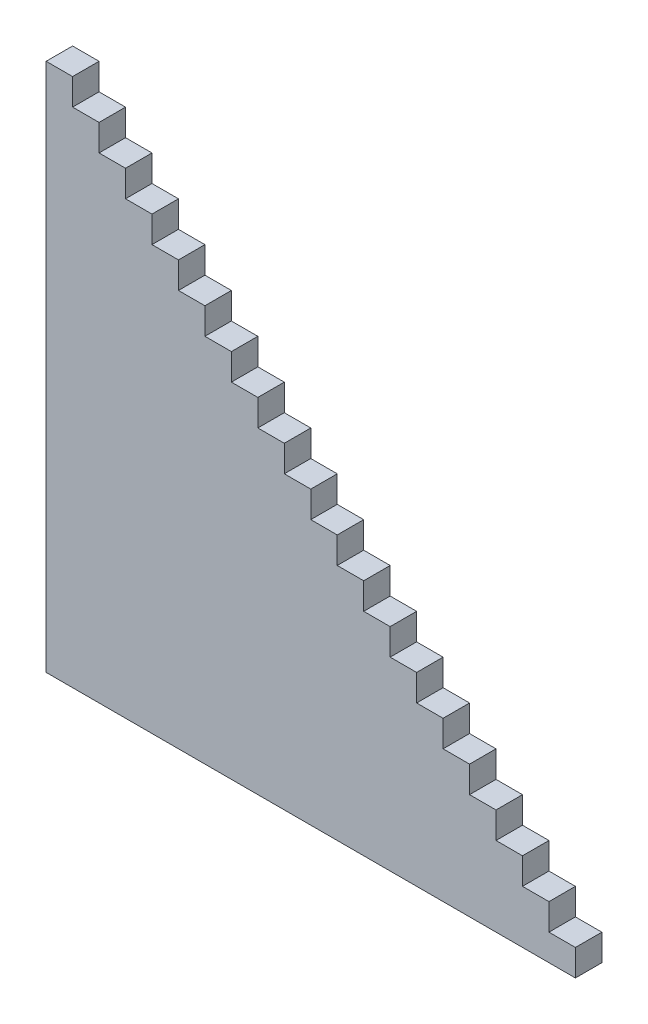
SolidWorks part; units mm, degrees
ref_plane "Front Plane" through (0, 0, 0) normal (0, 0, 1) x (1, 0, 0)
ref_plane "Top Plane" through (0, 0, 0) normal (0, 1, 0) x (1, 0, 0)
ref_plane "Right Plane" through (0, 0, 0) normal (1, 0, 0) x (0, 0, -1)
sketch "Sketch1" plane through (0, 0, 0) normal (0, 0, 1) x (1, 0, 0)
  line L8 (-79.0334, -42.191) -> (-77.0334, -42.191)
  line L9 (-79.0334, -42.191) -> (-79.0334, -44.191)
  line L10 (-79.0334, -82.191) -> (-39.0334, -82.191)
  line L30 (-79.0334, -44.191) -> (-79.0334, -46.191)
  line L31 (-79.0334, -46.191) -> (-79.0334, -48.191)
  line L32 (-79.0334, -48.191) -> (-79.0334, -50.191)
  line L33 (-79.0334, -50.191) -> (-79.0334, -52.191)
  line L34 (-79.0334, -52.191) -> (-79.0334, -54.191)
  line L35 (-79.0334, -54.191) -> (-79.0334, -56.191)
  line L36 (-79.0334, -56.191) -> (-79.0334, -58.191)
  line L37 (-79.0334, -58.191) -> (-79.0334, -60.191)
  line L38 (-79.0334, -60.191) -> (-79.0334, -62.191)
  line L39 (-79.0334, -62.191) -> (-79.0334, -64.191)
  line L40 (-79.0334, -64.191) -> (-79.0334, -66.191)
  line L41 (-79.0334, -66.191) -> (-79.0334, -68.191)
  line L42 (-79.0334, -68.191) -> (-79.0334, -70.191)
  line L43 (-79.0334, -70.191) -> (-79.0334, -72.191)
  line L44 (-79.0334, -72.191) -> (-79.0334, -74.191)
  line L45 (-79.0334, -74.191) -> (-79.0334, -76.191)
  line L46 (-79.0334, -76.191) -> (-79.0334, -78.191)
  line L47 (-79.0334, -78.191) -> (-79.0334, -80.191)
  line L48 (-79.0334, -80.191) -> (-79.0334, -82.191)
  line L49 (-77.0334, -44.191) -> (-75.0334, -44.191)
  line L50 (-75.0334, -46.191) -> (-73.0334, -46.191)
  line L68 (-77.0334, -42.191) -> (-77.0334, -44.191)
  line L69 (-75.0334, -44.191) -> (-75.0334, -46.191)
  line L83 (-73.0334, -48.191) -> (-71.0334, -48.191)
  line L85 (-71.0334, -50.191) -> (-69.0334, -50.191)
  line L86 (-69.0334, -52.191) -> (-67.0334, -52.191)
  line L88 (-73.0334, -46.191) -> (-73.0334, -48.191)
  line L89 (-67.0334, -54.191) -> (-65.0334, -54.191)
  line L90 (-71.0334, -48.191) -> (-71.0334, -50.191)
  line L92 (-69.0334, -50.191) -> (-69.0334, -52.191)
  line L94 (-67.0334, -52.191) -> (-67.0334, -54.191)
  line L95 (-65.0334, -54.191) -> (-65.0334, -56.191)
  line L96 (-65.0334, -56.191) -> (-63.0334, -56.191)
  line L98 (-63.0334, -56.191) -> (-63.0334, -58.191)
  line L99 (-63.0334, -58.191) -> (-61.0334, -58.191)
  line L100 (-61.0334, -58.191) -> (-61.0334, -60.191)
  line L102 (-59.0334, -60.191) -> (-59.0334, -62.191)
  line L103 (-61.0334, -60.191) -> (-59.0334, -60.191)
  line L104 (-57.0334, -62.191) -> (-57.0334, -64.191)
  line L106 (-55.0334, -64.191) -> (-55.0334, -66.191)
  line L107 (-59.0334, -62.191) -> (-57.0334, -62.191)
  line L108 (-53.0334, -66.191) -> (-53.0334, -68.191)
  line L110 (-51.0334, -68.191) -> (-51.0334, -70.191)
  line L111 (-57.0334, -64.191) -> (-55.0334, -64.191)
  line L112 (-49.0334, -70.191) -> (-49.0334, -72.191)
  line L114 (-47.0334, -72.191) -> (-47.0334, -74.191)
  line L115 (-55.0334, -66.191) -> (-53.0334, -66.191)
  line L116 (-45.0334, -74.191) -> (-45.0334, -76.191)
  line L118 (-43.0334, -76.191) -> (-43.0334, -78.191)
  line L119 (-53.0334, -68.191) -> (-51.0334, -68.191)
  line L120 (-41.0334, -78.191) -> (-41.0334, -80.191)
  line L121 (-39.0334, -80.191) -> (-39.0334, -82.191)
  line L123 (-51.0334, -70.191) -> (-49.0334, -70.191)
  line L125 (-49.0334, -72.191) -> (-47.0334, -72.191)
  line L126 (-43.0334, -44.191) -> (-43.0334, -46.191) [skipped]
  line L128 (-47.0334, -74.191) -> (-45.0334, -74.191)
  line L130 (-45.0334, -76.191) -> (-43.0334, -76.191)
  line L132 (-43.0334, -78.191) -> (-41.0334, -78.191)
  line L134 (-41.0334, -80.191) -> (-39.0334, -80.191)
  line L145 (-57.0334, -44.191) -> (-57.0334, -46.191) [skipped]
  line L146 (-73.0334, -42.191) -> (-73.0334, -44.191) [skipped]
  line L147 (-67.0334, -42.191) -> (-67.0334, -44.191) [skipped]
  line L148 (-65.0334, -42.191) -> (-65.0334, -44.191) [skipped]
  line L149 (-63.0334, -42.191) -> (-63.0334, -44.191) [skipped]
  line L150 (-61.0334, -42.191) -> (-61.0334, -44.191) [skipped]
  line L151 (-45.0334, -42.191) -> (-45.0334, -44.191) [skipped]
  line L152 (-47.0334, -44.191) -> (-47.0334, -46.191) [skipped]
  line L153 (-53.0334, -44.191) -> (-53.0334, -46.191) [skipped]
  line L154 (-55.0334, -44.191) -> (-55.0334, -46.191) [skipped]
  line L155 (-59.0334, -44.191) -> (-59.0334, -46.191) [skipped]
  line L156 (-71.0334, -44.191) -> (-71.0334, -46.191) [skipped]
  line L157 (-49.0334, -46.191) -> (-49.0334, -48.191) [skipped]
  line L185 (-69.0334, -46.191) -> (-69.0334, -48.191) [skipped]
  line L200 (-41.0334, -50.191) -> (-41.0334, -52.191) [skipped]
  line L201 (-51.0334, -46.191) -> (-51.0334, -48.191) [skipped]
  line L202 (-77.0334, -48.191) -> (-75.0334, -48.191) [skipped]
  line L203 (-77.0334, -80.191) -> (-43.0334, -80.191) [skipped]
  line L204 (-75.0334, -52.191) -> (-73.0334, -52.191) [skipped]
  line L205 (-75.0334, -50.191) -> (-73.0334, -50.191) [skipped]
  line L206 (-73.0334, -54.191) -> (-71.0334, -54.191) [skipped]
  line L207 (-73.0334, -56.191) -> (-71.0334, -56.191) [skipped]
  line L208 (-73.0334, -58.191) -> (-71.0334, -58.191) [skipped]
  line L209 (-75.0334, -60.191) -> (-73.0334, -60.191) [skipped]
  line L210 (-75.0334, -62.191) -> (-73.0334, -62.191) [skipped]
  line L211 (-77.0334, -76.191) -> (-75.0334, -76.191) [skipped]
  line L212 (-77.0334, -74.191) -> (-75.0334, -74.191) [skipped]
  line L213 (-77.0334, -72.191) -> (-75.0334, -72.191) [skipped]
  line L214 (-77.0334, -70.191) -> (-75.0334, -70.191) [skipped]
  line L215 (-77.0334, -68.191) -> (-75.0334, -68.191) [skipped]
  line L216 (-73.0334, -64.191) -> (-71.0334, -64.191) [skipped]
  line L217 (-71.0334, -66.191) -> (-67.0334, -66.191) [skipped]
  line L218 (-75.0334, -78.191) -> (-73.0334, -78.191) [skipped]
  dimension "D1" = 40
  dimension "D3" = 19
  dimension "D4" = 19
extrude "Boss-Extrude1" add sketch "Sketch1" along normal blind 2
